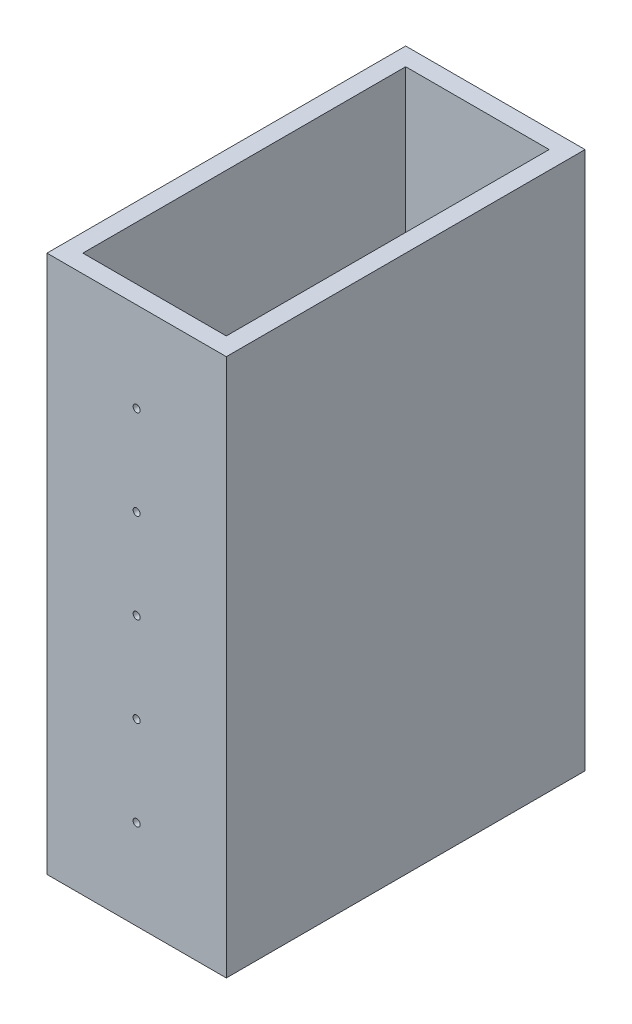
SolidWorks part; units mm, degrees
ref_plane "Front Plane" through (0, 0, 0) normal (0, 0, 1) x (1, 0, 0)
ref_plane "Top Plane" through (0, 0, 0) normal (0, 1, 0) x (1, 0, 0)
ref_plane "Right Plane" through (0, 0, 0) normal (1, 0, 0) x (0, 0, -1)
sketch "Sketch1" plane through (0, 0, 0) normal (0, 1, 0) x (1, 0, 0)
  line L1 (0, 0) -> (25.4, 0)
  line L2 (0, 0) -> (0, 50.8)
  line L3 (0, 50.8) -> (25.4, 50.8)
  line L4 (25.4, 0) -> (25.4, 50.8)
  line L5 (2.54, 2.54) -> (22.86, 2.54)
  line L6 (2.54, 2.54) -> (2.54, 48.26)
  line L7 (2.54, 48.26) -> (22.86, 48.26)
  line L8 (22.86, 2.54) -> (22.86, 48.26)
  line L9 (2.54, 2.54) -> (22.86, 48.26) construction
  line L10 (2.54, 48.26) -> (22.86, 2.54) construction
  point P4 (12.7, 25.4)
  dimension "D1" = 50.8
  dimension "D2" = 25.4
  dimension "D3" = 45.72
  dimension "D4" = 20.32
  dimension "D5" = 2.54
  dimension "D6" = 2.54
extrude "Boss-Extrude1" add sketch "Sketch1" along normal blind 76.2
sketch "Sketch2" plane through (0, 0, -50.8) normal (0, 0, -1) x (-1, 0, 0)
  line L0 (-25.4, 0) -> (0, 0) construction
  line L1 (0, 76.2) -> (0, 0) construction
  circle A0 centre (-12.7, 12.7) radius 0.5
  circle A1 centre (-12.7, 25.4) radius 0.5
  circle A2 centre (-12.7, 38.1) radius 0.5
  circle A3 centre (-12.7, 50.8) radius 0.5
  circle A4 centre (-12.7, 63.5) radius 0.5
  dimension "D1" = 1
  dimension "D3" = 12.7
  dimension "D2" = 12.7
  dimension "D4" = 5
extrude "Cut-Extrude1" cut sketch "Sketch2" against normal blind 76.2
